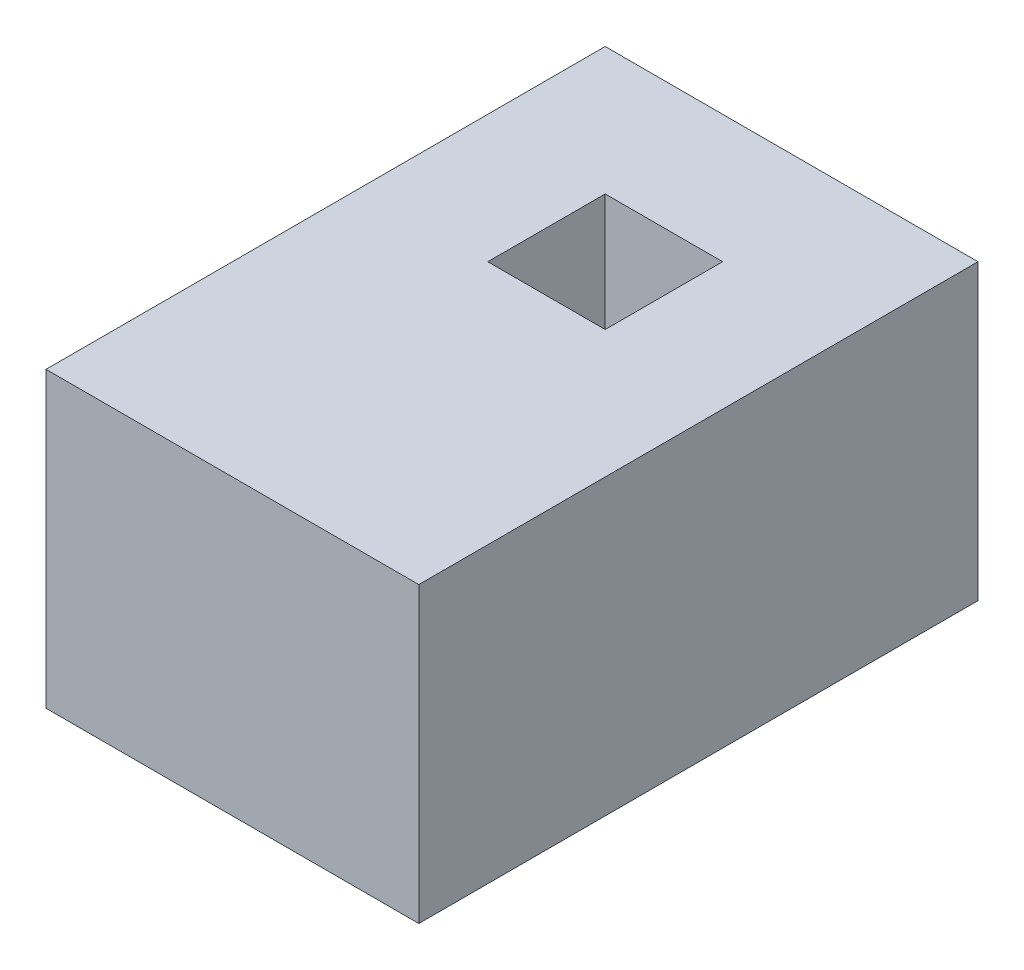
SolidWorks part; units mm, degrees
ref_plane "Front Plane" through (0, 0, 0) normal (0, 0, 1) x (1, 0, 0)
ref_plane "Top Plane" through (0, 0, 0) normal (0, 1, 0) x (1, 0, 0)
ref_plane "Right Plane" through (0, 0, 0) normal (1, 0, 0) x (0, 0, -1)
sketch "Sketch1" plane through (0, 0, 0) normal (0, 1, 0) x (1, 0, 0)
  line L0 (0, 0) -> (0, 0.3175) construction
  line L1 (-0.635, -0.9525) -> (0.635, -0.9525)
  line L2 (-0.635, -0.9525) -> (-0.635, 0.9525)
  line L3 (-0.635, 0.9525) -> (0.635, 0.9525)
  line L4 (0.635, -0.9525) -> (0.635, 0.9525)
  line L5 (-0.635, -0.9525) -> (0.635, 0.9525) construction
  line L6 (-0.635, 0.9525) -> (0.635, -0.9525) construction
  line L7 (-0.2, 0.5175) -> (0.2, 0.5175)
  line L8 (-0.2, 0.5175) -> (-0.2, 0.1175)
  line L9 (-0.2, 0.1175) -> (0.2, 0.1175)
  line L10 (0.2, 0.5175) -> (0.2, 0.1175)
  line L11 (-0.2, 0.5175) -> (0.2, 0.1175) construction
  line L12 (-0.2, 0.1175) -> (0.2, 0.5175) construction
  point P0 (0, 0)
  point P6 (0, 0.3175)
  dimension "D1" = 1.27
  dimension "D2" = 1.905
  dimension "D3" = 0.4
  dimension "D4" = 0.4
  dimension "D5" = 0.635
extrude "Boss-Extrude1" add sketch "Sketch1" along normal blind 1
equation "\"D5@Sketch1\"=1.27/2"
